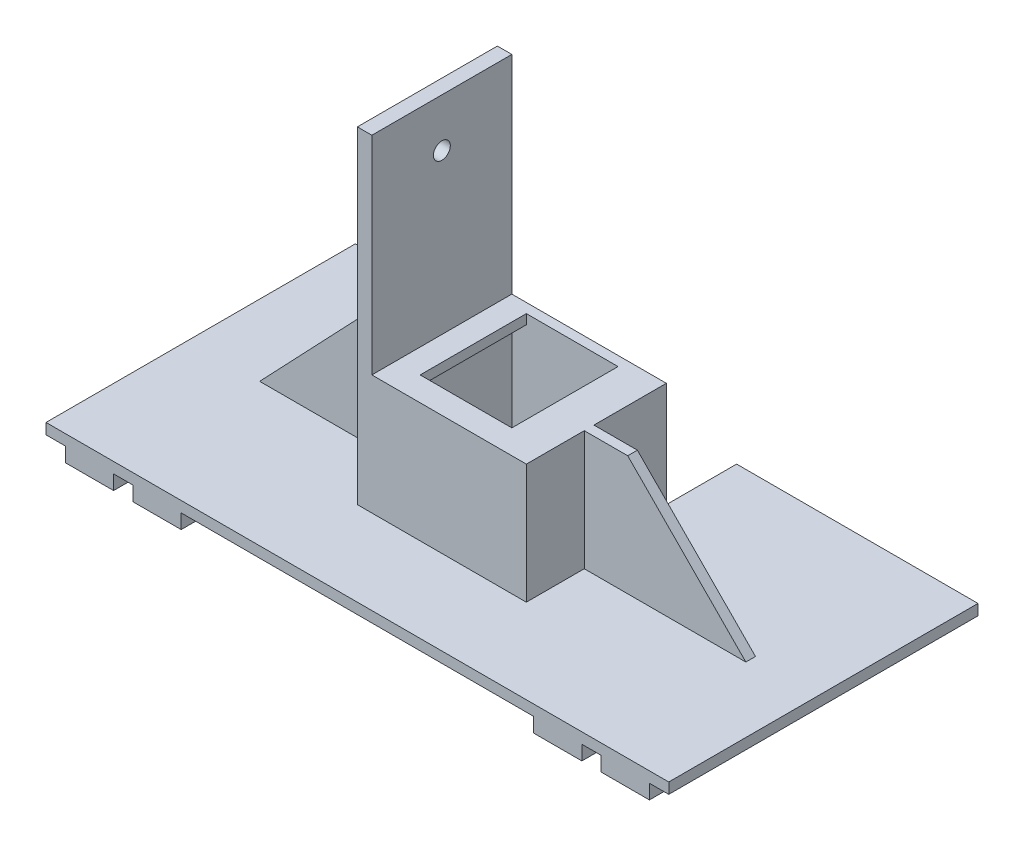
SolidWorks part; units mm, degrees
ref_plane "Front Plane" through (0, 0, 0) normal (0, 0, 1) x (1, 0, 0)
ref_plane "Top Plane" through (0, 0, 0) normal (0, 1, 0) x (1, 0, 0)
ref_plane "Right Plane" through (0, 0, 0) normal (1, 0, 0) x (0, 0, -1)
sketch "Sketch1" plane through (0, 0, 0) normal (0, 0, 1) x (1, 0, 0)
  line L1 (0, 0) -> (29, 0)
  line L2 (0, 0) -> (0, 27)
  line L3 (0, 27) -> (29, 27)
  line L4 (29, 0) -> (29, 27)
  dimension "D1" = 27
  dimension "D2" = 29
extrude "Boss-Extrude2" add sketch "Sketch1" along normal blind 2
sketch "Sketch2" plane through (0, 0, 0) normal (0, 0, 1) x (1, 0, 0)
  line L1 (0, 0) -> (29, 0) construction
  line L2 (0, 27) -> (2, 27)
  line L3 (0, 27) -> (0, 0)
  line L4 (0, 0) -> (2, 0)
  line L5 (2, 27) -> (2, 0)
  dimension "D1" = 2
extrude "Boss-Extrude3" add sketch "Sketch2" against normal blind 27
sketch "Sketch3" plane through (0, 0, 0) normal (0, 0, 1) x (1, 0, 0)
  line L0 (0, 0) -> (29, 0) construction
  line L1 (29, 27) -> (27, 27)
  line L2 (29, 27) -> (29, 0)
  line L3 (29, 0) -> (27, 0)
  line L4 (27, 27) -> (27, 0)
  dimension "D1" = 2
extrude "Boss-Extrude4" add sketch "Sketch3" against normal blind 27
sketch "Sketch4" plane through (0, 0, 0) normal (1, 0, 0) x (0, 0, -1)
  line L0 (-2, 0) -> (27, 0) construction
  line L1 (27, 27) -> (25, 27)
  line L2 (27, 27) -> (27, 0)
  line L3 (27, 0) -> (25, 0)
  line L4 (25, 27) -> (25, 0)
  dimension "D1" = 2
extrude "Boss-Extrude5" add sketch "Sketch4" along normal blind 29
sketch "Sketch5" plane through (0, 0, 0) normal (1, 0, 0) x (0, 0, -1)
  line L0 (27, 0) -> (27, 27) construction
  line L1 (-2, 27) -> (27, 27)
  line L2 (-2, 27) -> (-2, 25)
  line L3 (-2, 25) -> (27, 25)
  line L4 (27, 27) -> (27, 25)
  dimension "D1" = 2
extrude "Boss-Extrude6" add sketch "Sketch5" along normal blind 5
ref_plane "Plane1" through (29, 0, 0) normal (1, 0, 0) x (0, 0, -1)
sketch "Sketch6" plane through (29, 0, 0) normal (1, 0, 0) x (0, 0, -1)
  line L0 (27, 0) -> (27, 27) construction
  line L1 (-2, 27) -> (27, 27)
  line L2 (-2, 27) -> (-2, 25)
  line L3 (-2, 25) -> (27, 25)
  line L4 (27, 27) -> (27, 25)
  dimension "D1" = 2
extrude "Boss-Extrude7" add sketch "Sketch6" against normal blind 5
sketch "Sketch7" plane through (0, 0, 0) normal (0, 0, 1) x (1, 0, 0)
  line L0 (29, 27) -> (0, 27) construction
  line L1 (0, 27) -> (29, 27)
  line L2 (0, 27) -> (0, 25)
  line L3 (0, 25) -> (29, 25)
  line L4 (29, 27) -> (29, 25)
  line L5 (29, -14.85) -> (29, 14.85) construction
  dimension "D1" = 2
extrude "Boss-Extrude9" add sketch "Sketch7" against normal blind 3
sketch "Sketch8" plane through (0, 0, 0) normal (1, 0, 0) x (0, 0, -1)
  line L1 (-2, 0) -> (27, 0)
  line L2 (-2, 0) -> (-2, 70)
  line L3 (-2, 70) -> (27, 70)
  line L4 (27, 0) -> (27, 70)
  dimension "D1" = 70
  dimension "D2" = 29
extrude "Boss-Extrude10" add sketch "Sketch8" against normal blind 3
sketch "Sketch9" plane through (29, 0, 0) normal (1, 0, 0) x (0, 0, -1)
  line L1 (-2, 70) -> (27, 70)
  line L2 (-2, 70) -> (-2, 0)
  line L3 (-2, 0) -> (27, 0)
  line L4 (27, 70) -> (27, 0)
extrude "Boss-Extrude11" add sketch "Sketch9" along normal blind 3
sketch "Sketch10" plane through (0, 0, 0) normal (1, 0, 0) x (0, 0, -1)
  line L0 (27, 0) -> (27, 70) construction
  line L1 (27, 70) -> (-2, 70) construction
  circle A1 centre (12.5, 60) radius 1.75
  dimension "D2" = 3.5
  dimension "D3" = 14.5
  dimension "D6" = 10
extrude "Cut-Extrude1" cut sketch "Sketch10" against normal blind 4 and the other way blind 40
sketch "Sketch14" plane through (29, 0, 0) normal (1, 0, 0) x (0, 0, -1)
  line L1 (-19.5, 0) -> (44.5592, 0)
  line L2 (-19.5, 0) -> (-19.5, 2.2282)
  line L3 (-19.5, 2.2282) -> (44.5592, 2.2282)
  line L4 (44.5592, 0) -> (44.5592, 2.2282)
  dimension "D1" = 17.5
extrude "Boss-Extrude15" add sketch "Sketch14" along normal blind 50
ref_plane "Plane6" through (0, 0, 0) normal (1, 0, 0) x (0, 0, -1)
sketch "Sketch15" plane through (0, 0, 0) normal (1, 0, 0) x (0, 0, -1)
  line L1 (-19.5, 2.2282) -> (44.5592, 2.2282)
  line L2 (-19.5, 2.2282) -> (-19.5, 0)
  line L3 (-19.5, 0) -> (44.5592, 0)
  line L4 (44.5592, 2.2282) -> (44.5592, 0)
extrude "Boss-Extrude16" add sketch "Sketch15" against normal blind 50
sketch "Sketch16" plane through (0, 0, 0) normal (1, 0, 0) x (0, 0, -1)
  line L1 (-19.5, 2.2282) -> (-2, 2.2282)
  line L2 (-19.5, 2.2282) -> (-19.5, 0)
  line L3 (-19.5, 0) -> (-2, 0)
  line L4 (-2, 2.2282) -> (-2, 0)
extrude "Boss-Extrude17" add sketch "Sketch16" along normal blind 29
ref_plane "Plane7" through (0, 0, -11) normal (0, 0, 1) x (1, 0, 0)
sketch "Sketch18" plane through (0, 0, -11) normal (0, 0, 1) x (1, 0, 0)
  line L0 (-35.2418, 2.2282) -> (-3, 2.2282)
  line L1 (79, 2.2282) -> (-50, 2.2282) construction
  line L2 (-3, 2.2282) -> (-3, 36.1141)
  line L3 (-3, 70) -> (-3, 2.2282) construction
  line L4 (-3, 36.1141) -> (-35.2418, 2.2282)
  line L5 (32, 2.2282) -> (65.4713, 2.2282)
  line L6 (65.4713, 2.2282) -> (32, 36.1141)
  line L7 (32, 70) -> (32, 2.2282) construction
  line L8 (32, 36.1141) -> (32, 2.2282)
extrude "Boss-Extrude18" add sketch "Sketch18" along normal blind 1 and the other way blind 1
sketch "Sketch19" plane through (29, 0, 0) normal (1, 0, 0) x (0, 0, -1)
  line L0 (27, 2.2282) -> (27, 70) construction
  line L1 (-2, 70) -> (27, 70)
  line L2 (-2, 70) -> (-2, 27)
  line L3 (-2, 27) -> (27, 27)
  line L4 (27, 70) -> (27, 27)
  dimension "D1" = 43
extrude "Cut-Extrude2" cut sketch "Sketch19" along normal blind 15
sketch "Sketch20" plane through (0, 0, 0) normal (0, 1, 0) x (1, 0, 0)
  line L0 (-50, 44.5592) -> (0, 44.5592) construction
  line L1 (-46, 44.5592) -> (-36, 44.5592)
  line L2 (-46, 44.5592) -> (-46, -19.5)
  line L3 (-46, -19.5) -> (-36, -19.5)
  line L4 (-36, 44.5592) -> (-36, -19.5)
  line L5 (79, -19.5) -> (-50, -19.5) construction
  line L6 (79, 44.5592) -> (29, 44.5592) construction
  line L7 (-32, 44.5592) -> (-22, 44.5592)
  line L8 (-32, 44.5592) -> (-32, -19.5)
  line L9 (-32, -19.5) -> (-22, -19.5)
  line L10 (-22, 44.5592) -> (-22, -19.5)
  line L11 (75, 44.5592) -> (65, 44.5592)
  line L12 (75, 44.5592) -> (75, -19.5)
  line L13 (75, -19.5) -> (65, -19.5)
  line L14 (65, 44.5592) -> (65, -19.5)
  line L15 (-50, 44.5592) -> (-50, -19.5) construction
  line L16 (61, 44.5592) -> (51, 44.5592)
  line L17 (61, 44.5592) -> (61, -19.5)
  line L18 (61, -19.5) -> (51, -19.5)
  line L19 (51, 44.5592) -> (51, -19.5)
  line L20 (79, 44.5592) -> (79, -19.5) construction
  dimension "D1" = 10
  dimension "D2" = 10
  dimension "D3" = 10
  dimension "D4" = 10
  dimension "D5" = 4
  dimension "D6" = 4
  dimension "D7" = 4
  dimension "D8" = 4
extrude "Boss-Extrude19" add sketch "Sketch20" against normal blind 3
sketch "Sketch21" plane through (0, 0, 0) normal (0, 1, 0) x (1, 0, 0)
  line L2 (-46, -19.5) -> (-36, -19.5) construction
  line L3 (-36, 44.5592) -> (-46, 44.5592) construction
  line L4 (-36, -19.5) -> (-36, 44.5592) construction
  line L5 (-32, 44.5592) -> (-32, -19.5) construction
  line L6 (51, 44.5592) -> (51, -19.5) construction
  line L7 (75, -19.5) -> (75, 44.5592) construction
  circle A0 centre (-41, 29.5592) radius 1.75
  circle A1 centre (-41, 12.5592) radius 1.75
  circle A2 centre (-41, -4.5) radius 1.75
  circle A3 centre (-27, 29.5592) radius 1.75
  circle A4 centre (-27, 12.5592) radius 1.75
  circle A5 centre (-27, -4.5) radius 1.75
  circle A6 centre (56, 29.5592) radius 1.75
  circle A7 centre (56, 12.5592) radius 1.75
  circle A8 centre (56, -4.5) radius 1.75
  circle A9 centre (70, 29.5592) radius 1.75
  circle A10 centre (70, 12.5592) radius 1.75
  circle A11 centre (70, -4.5) radius 1.75
  dimension "D1" = 3.5
  dimension "D2" = 3.5
  dimension "D3" = 3.5
  dimension "D7" = 3.5
  dimension "D8" = 3.5
  dimension "D9" = 3.5
  dimension "D18" = 3.5
  dimension "D19" = 3.5
  dimension "D20" = 3.5
  dimension "D22" = 3.5
  dimension "D23" = 3.5
  dimension "D24" = 3.5
  dimension "D4" = 15
  dimension "D5" = 15
  dimension "D6" = 17
  dimension "D10" = 17
  dimension "D11" = 5
  dimension "D12" = 5
  dimension "D13" = 5
  dimension "D14" = 5
  dimension "D15" = 5
  dimension "D16" = 5
  dimension "D17" = 5
  dimension "D21" = 5
extrude "Boss-Extrude20" add sketch "Sketch21" against normal blind 4
